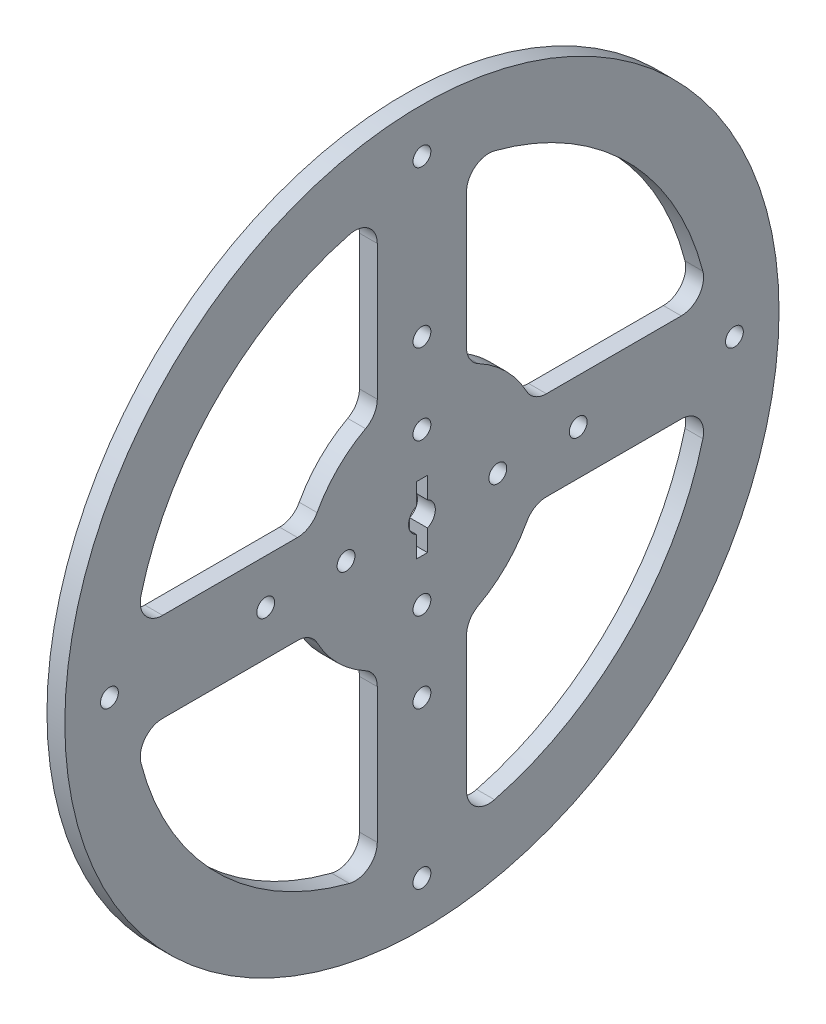
SolidWorks part; units mm, degrees
ref_plane "Front Plane" through (0, 0, 0) normal (0, 0, 1) x (1, 0, 0)
ref_plane "Top Plane" through (0, 0, 0) normal (0, 1, 0) x (1, 0, 0)
ref_plane "Right Plane" through (0, 0, 0) normal (1, 0, 0) x (0, 0, -1)
sketch "Sketch1" plane through (0, 0, 0) normal (1, 0, 0) x (0, 0, -1)
  line L0 (0, 73.3847) -> (0, -70.9537) construction
  line L1 (-10, 27.8862) -> (-10, 58.0948)
  line L3 (-10, -58.0948) -> (-10, -27.8862)
  line L5 (10, -58.0948) -> (10, -27.8862)
  line L14 (10, 27.8862) -> (10, 58.0948)
  line L15 (-27.8862, 10) -> (-58.0948, 10)
  line L16 (-27.8862, -10) -> (-58.0948, -10)
  line L18 (58.0948, -10) -> (27.8862, -10)
  line L19 (58.0948, 10) -> (27.8862, 10)
  circle A0 centre (0, 0) radius 80
  circle A2 centre (0, 17) radius 2
  circle A3 centre (0, 35) radius 2
  circle A4 centre (0, 70) radius 2
  arc A5 (-16.25, 62.936) -> (-62.936, 16.25) centre (0, 0) ccw
  arc A6 (-12.6314, 23.4828) -> (-23.4828, 12.6314) centre (0, 0) ccw
  arc A7 (-23.4828, -12.6314) -> (-12.6314, -23.4828) centre (0, 0) ccw
  arc A8 (-62.936, -16.25) -> (-16.25, -62.936) centre (0, 0) ccw
  arc A9 (23.4828, 12.6314) -> (12.6314, 23.4828) centre (0, 0) ccw
  arc A10 (12.6314, -23.4828) -> (23.4828, -12.6314) centre (0, 0) ccw
  arc A11 (62.936, 16.25) -> (16.25, 62.936) centre (0, 0) ccw
  arc A12 (16.25, -62.936) -> (62.936, -16.25) centre (0, 0) ccw
  arc A13 (10, -58.0948) -> (16.25, -62.936) centre (15, -58.0948) ccw
  arc A14 (-10, -58.0948) -> (-16.25, -62.936) centre (-15, -58.0948) cw
  arc A15 (-58.0948, -10) -> (-62.936, -16.25) centre (-58.0948, -15) ccw
  arc A16 (-23.4828, -12.6314) -> (-27.8862, -10) centre (-27.8862, -15) ccw
  arc A17 (-12.6314, -23.4828) -> (-10, -27.8862) centre (-15, -27.8862) cw
  arc A18 (10, -27.8862) -> (12.6314, -23.4828) centre (15, -27.8862) cw
  arc A19 (23.4828, -12.6314) -> (27.8862, -10) centre (27.8862, -15) cw
  arc A20 (58.0948, -10) -> (62.936, -16.25) centre (58.0948, -15) cw
  arc A21 (62.936, 16.25) -> (58.0948, 10) centre (58.0948, 15) cw
  arc A22 (27.8862, 10) -> (23.4828, 12.6314) centre (27.8862, 15) cw
  arc A23 (12.6314, 23.4828) -> (10, 27.8862) centre (15, 27.8862) cw
  arc A24 (10, 58.0948) -> (16.25, 62.936) centre (15, 58.0948) cw
  arc A25 (-58.0948, 10) -> (-62.936, 16.25) centre (-58.0948, 15) cw
  arc A26 (-27.8862, 10) -> (-23.4828, 12.6314) centre (-27.8862, 15) ccw
  arc A27 (-10, 27.8862) -> (-12.6314, 23.4828) centre (-15, 27.8862) cw
  arc A28 (-10, 58.0948) -> (-16.25, 62.936) centre (-15, 58.0948) ccw
  circle A29 centre (70, 0) radius 2
  circle A30 centre (35, 0) radius 2
  circle A31 centre (0, -70) radius 2
  circle A32 centre (0, -35) radius 2
  circle A33 centre (-70, 0) radius 2
  circle A34 centre (-35, 0) radius 2
  circle A36 centre (17, 0) radius 2
  circle A38 centre (0, -17) radius 2
  circle A39 centre (0, 0) radius 3
  circle A40 centre (-17, 0) radius 2
  point P38 (10, -64.2262)
  point P43 (-64.2262, -10)
  point P50 (10, -24.7183)
  point P59 (24.7183, 10)
  point P62 (10, 24.7183)
  point P88 (0, 0)
  point P98 (0, 0)
  dimension "D1" = 160
  dimension "D4" = 4
  dimension "D5" = 4
  dimension "D6" = 4
  dimension "D9" = 130
  dimension "D11" = 5
  dimension "D3" = 70
  dimension "D7" = 35
  dimension "D8" = 17
  dimension "D10" = 20
  dimension "D12" = 4
  dimension "D13" = 4
extrude "Boss-Extrude1" add sketch "Sketch1" along normal blind 4
sketch "Sketch2" plane through (0, 0, 0) normal (-1, 0, 0) x (0, 0, 1)
  line L1 (-1.25, -7.5) -> (1.25, -7.5)
  line L2 (-1.25, -7.5) -> (-1.25, 7.5)
  line L3 (-1.25, 7.5) -> (1.25, 7.5)
  line L4 (1.25, -7.5) -> (1.25, 7.5)
  line L5 (-1.25, -7.5) -> (1.25, 7.5) construction
  line L6 (-1.25, 7.5) -> (1.25, -7.5) construction
  point P0 (0, 0)
  dimension "D1" = 15
  dimension "D2" = 2.5
extrude "Cut-Extrude1" cut sketch "Sketch2" against normal blind 10
